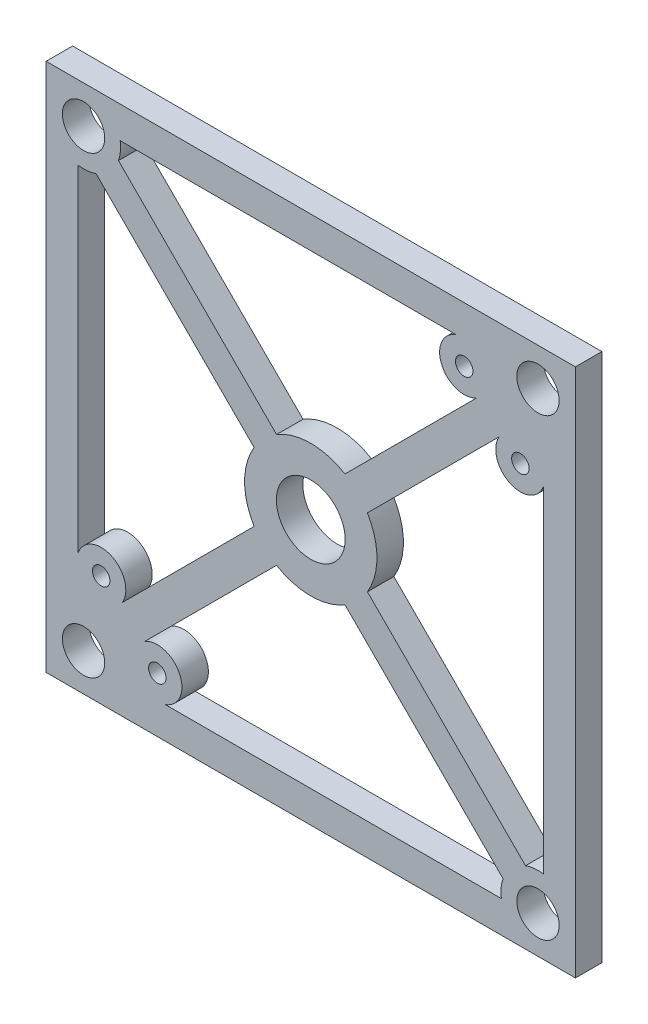
SolidWorks part; units mm, degrees
ref_plane "Front Plane" through (0, 0, 0) normal (0, 0, 1) x (1, 0, 0)
ref_plane "Top Plane" through (0, 0, 0) normal (0, 1, 0) x (1, 0, 0)
ref_plane "Right Plane" through (0, 0, 0) normal (1, 0, 0) x (0, 0, -1)
sketch "Sketch1" plane through (0, 0, 0) normal (0, 0, 1) x (1, 0, 0)
  line L1 (-50, -50) -> (50, -50)
  line L2 (-50, -50) -> (-50, 50)
  line L3 (-50, 50) -> (50, 50)
  line L4 (50, -50) -> (50, 50)
  line L5 (-50, -50) -> (50, 50) construction
  line L6 (-50, 50) -> (50, -50) construction
  point P0 (0, 0)
  dimension "D1" = 100
  dimension "D2" = 100
extrude "MainBody" add sketch "Sketch1" along normal blind 5
sketch "Sketch2" plane through (0, 0, 5) normal (0, 0, 1) x (1, 0, 0)
  line L0 (0, 0) -> (42.9289, 42.9289) construction
  line L1 (42.9289, 42.9289) -> (50, 50) construction
  line L2 (0, 0) -> (42.9289, -42.9289) construction
  line L3 (42.9289, -42.9289) -> (50, -50) construction
  line L4 (0, 0) -> (-42.9289, -42.9289) construction
  line L5 (-42.9289, -42.9289) -> (-50, -50) construction
  line L6 (0, 0) -> (-42.9289, 42.9289) construction
  line L7 (-42.9289, 42.9289) -> (-50, 50) construction
  circle A0 centre (0, 0) radius 6.5
  circle A1 centre (-42.9289, -42.9289) radius 4
  circle A2 centre (42.9289, -42.9289) radius 4
  circle A3 centre (42.9289, 42.9289) radius 4
  circle A4 centre (-42.9289, 42.9289) radius 4
  dimension "D1" = 13
  dimension "D2" = 8
  dimension "D3" = 10
extrude "Bearing&BushingHoles" cut sketch "Sketch2" against normal through all
hole_wizard "M4 Tapped Hole1" positions "3DSketch1" profile "Sketch4" tap size "M4" standard "ISO" end condition through all
sketch3d "3DSketch1"
  line L0 (0, 0, 0) -> (34.2947, 34.2947, 0) construction
  line L1 (34.2947, 34.2947, 0) -> (28.9914, 39.598, 0) construction
  line L3 (34.2947, 34.2947, 0) -> (39.598, 28.9914, 0) construction
  line L5 (0, 0, 0) -> (-34.2947, -34.2947, 0) construction
  line L6 (-34.2947, -34.2947, 0) -> (-39.598, -28.9914, 0) construction
  line L8 (-34.2947, -34.2947, 0) -> (-28.9914, -39.598, 0) construction
  line L12 (34.2947, 34.2947, 0) -> (42.9289, 42.9289, 0) construction
  line L14 (-34.2947, -34.2947, 0) -> (-42.9289, -42.9289, 0) construction
  circle A0 centre (0, 0, 0) radius 6.5 construction
  circle A1 centre (0, 0, 0) radius 6.5 construction
  circle A6 centre (42.9289, 42.9289, 0) radius 4 construction
  circle A7 centre (-42.9289, -42.9289, 0) radius 4 construction
  circle A8 centre (42.9289, 42.9289, 0) radius 4
  circle A9 centre (-42.9289, -42.9289, 0) radius 4
  point P0 (-39.598, -28.9914, 0)
  point P2 (-28.9914, -39.598, 0)
  point P4 (28.9914, 39.598, 0)
  point P6 (39.598, 28.9914, 0)
  point P19 (0, 0, 6.5)
  point P21 (0, 0, 6.5)
  point P45 (42.9289, 42.9289, 4)
  point P48 (-42.9289, -42.9289, 4)
  point P50 (42.9289, 42.9289, 4)
  point P52 (-42.9289, -42.9289, 4)
  dimension "D1" = 15
  dimension "D2" = 97
sketch "Sketch4" plane through (-39.598, -28.9914, 0) normal (1, 0, 0) x (0, 1, 0)
  line L0 (0, 0) -> (0, 5)
  line L1 (0, 5) -> (1.65, 5)
  line L2 (1.65, 5) -> (1.65, 0)
  line L5 (1.65, 0) -> (0, 0)
  line L11 (0, -6.35) -> (0, 107.95) construction
  dimension "Thru Tap Drill Dia." = 3.3
  dimension "Thru Tap Drill Depth" = 5
cosmetic thread "Hole Thread1" parameters "D2"=4
cosmetic thread "Hole Thread2" parameters "D2"=4
cosmetic thread "Hole Thread3" parameters "D2"=4
cosmetic thread "Hole Thread4" parameters "D2"=4
sketch "Sketch5" plane through (0, 0, 0) normal (0, 0, -1) x (-1, 0, 0)
  line L0 (6.5, 0) -> (12.5, 0) construction
  line L1 (0, 0) -> (50, 50) construction
  line L2 (0, 0) -> (-50, -50) construction
  line L3 (0, 0) -> (50, -50) construction
  line L4 (0, 0) -> (-50, 50) construction
  line L5 (-44, 27.4931) -> (-44, -36.0114)
  line L6 (-40.5781, -36.3355) -> (-38.4568, -38.4568) construction
  line L7 (44, -27.4931) -> (44, 36.0114)
  line L8 (-27.4931, 44) -> (36.0114, 44)
  line L9 (-38.4568, -38.4568) -> (-36.3355, -40.5781) construction
  line L10 (50, -50) -> (-50, -50) construction
  line L11 (10.7018, -6.4592) -> (35.5876, -31.345)
  line L12 (6.4592, -10.7018) -> (31.345, -35.5876)
  line L13 (-50, -50) -> (-50, 50) construction
  line L14 (-36.3355, -40.5781) -> (-6.4592, -10.7018)
  line L15 (50, 50) -> (50, -50) construction
  line L16 (-40.5781, -36.3355) -> (-10.7018, -6.4592)
  line L17 (-36.0114, -44) -> (27.4931, -44)
  line L18 (31.345, -35.5876) -> (33.4663, -33.4663) construction
  line L19 (33.4663, -33.4663) -> (35.5876, -31.345) construction
  line L20 (-50, 50) -> (50, 50) construction
  line L21 (6.4592, 10.7018) -> (36.3355, 40.5781)
  line L22 (10.7018, 6.4592) -> (40.5781, 36.3355)
  line L23 (40.5781, 36.3355) -> (38.4568, 38.4568) construction
  line L24 (38.4568, 38.4568) -> (36.3355, 40.5781) construction
  line L25 (-31.345, 35.5876) -> (-6.4592, 10.7018)
  line L26 (-10.7018, 6.4592) -> (-35.5876, 31.345)
  line L27 (-35.5876, 31.345) -> (-33.4663, 33.4663) construction
  line L28 (-33.4663, 33.4663) -> (-31.345, 35.5876) construction
  arc A0 (-6.4592, -10.7018) -> (6.4592, -10.7018) centre (0, 0) ccw
  circle A1 centre (0, 0) radius 6.5 construction
  circle A2 centre (-42.9289, -42.9289) radius 4 construction
  circle A3 centre (-42.9289, -42.9289) radius 4 construction
  arc A5 (-40.5781, -36.3355) -> (-44, -36.0114) centre (-42.9289, -42.9289) ccw
  arc A6 (-36.0114, -44) -> (-36.3355, -40.5781) centre (-42.9289, -42.9289) ccw
  circle A7 centre (28.9914, -39.598) radius 1.65 construction
  circle A8 centre (28.9914, -39.598) radius 1.65
  circle A9 centre (39.598, -28.9914) radius 1.65 construction
  circle A10 centre (39.598, -28.9914) radius 1.65
  arc A12 (44, -27.4931) -> (35.5876, -31.345) centre (39.598, -28.9914) ccw
  circle A13 centre (42.9289, -42.9289) radius 4 construction
  circle A14 centre (42.9289, -42.9289) radius 4 construction
  arc A16 (31.345, -35.5876) -> (27.4931, -44) centre (28.9914, -39.598) ccw
  arc A17 (10.7018, -6.4592) -> (10.7018, 6.4592) centre (0, 0) ccw
  circle A18 centre (42.9289, 42.9289) radius 4 construction
  circle A19 centre (42.9289, 42.9289) radius 4
  arc A20 (36.0114, 44) -> (36.3355, 40.5781) centre (42.9289, 42.9289) ccw
  arc A21 (40.5781, 36.3355) -> (44, 36.0114) centre (42.9289, 42.9289) ccw
  arc A22 (6.4592, 10.7018) -> (-6.4592, 10.7018) centre (0, 0) ccw
  circle A23 centre (-39.598, 28.9914) radius 1.65 construction
  circle A24 centre (-28.9914, 39.598) radius 1.65 construction
  circle A25 centre (-39.598, 28.9914) radius 1.65
  circle A26 centre (-28.9914, 39.598) radius 1.65
  arc A27 (-31.345, 35.5876) -> (-27.4931, 44) centre (-28.9914, 39.598) ccw
  arc A28 (-44, 27.4931) -> (-35.5876, 31.345) centre (-39.598, 28.9914) ccw
  arc A29 (-10.7018, 6.4592) -> (-10.7018, -6.4592) centre (0, 0) ccw
  dimension "D2" = 3
  dimension "D6" = 3
  dimension "D7" = 6
  dimension "D10" = 3
  dimension "D12" = 3
  dimension "D13" = 3
  dimension "D1" = 6
  dimension "D3" = 6
  dimension "D4" = 6
  dimension "D5" = 6
  dimension "D8" = 6
  dimension "D9" = 6
  dimension "D11" = 6
  dimension "D14" = 6
extrude "Cut-Extrude1" cut sketch "Sketch5" against normal through all
